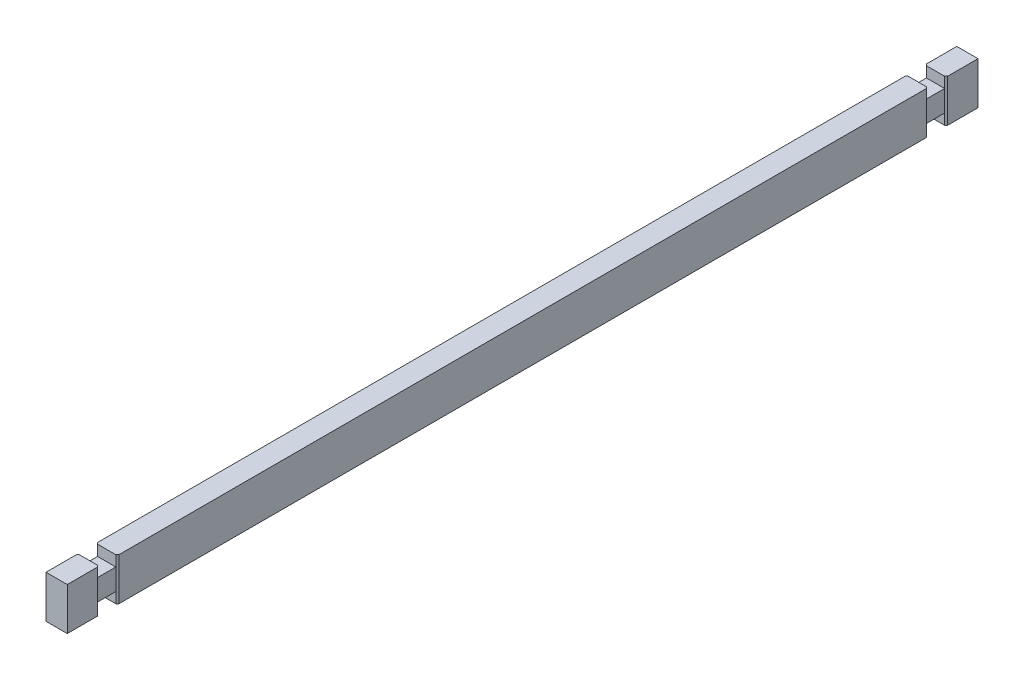
SolidWorks part; units mm, degrees
ref_plane "Front Plane" through (0, 0, 0) normal (0, 0, 1) x (1, 0, 0)
ref_plane "Top Plane" through (0, 0, 0) normal (0, 1, 0) x (1, 0, 0)
ref_plane "Right Plane" through (0, 0, 0) normal (1, 0, 0) x (0, 0, -1)
sketch "Sketch1" plane through (0, 0, 0) normal (0, 0, 1) x (1, 0, 0)
  line L1 (-35, 70) -> (35, 70)
  line L2 (-35, 70) -> (-35, -70)
  line L3 (-35, -70) -> (35, -70)
  line L4 (35, 70) -> (35, -70)
  dimension "D1" = 140
  dimension "D2" = 70
  dimension "D3" = 35
  dimension "D4" = 70
extrude "Extrude1" add sketch "Sketch1" along normal blind 3000
sketch "Sketch2" plane through (0, 70, 0) normal (0, 1, 0) x (-1, 0, 0)
  line L0 (35, 100) -> (30, 105)
  line L1 (35, 3000) -> (35, 0) construction
  line L2 (30, 165) -> (30, 105)
  line L3 (30, 165) -> (35, 170)
  line L4 (-35, 100) -> (-30, 105)
  line L5 (-35, 3000) -> (-35, 0) construction
  line L6 (-30, 105) -> (-30, 165)
  line L7 (-30, 165) -> (-35, 170)
  line L8 (-35, 100) -> (-35, 170)
  line L9 (35, 100) -> (35, 170)
  line L10 (-35, 0) -> (35, 0) construction
  dimension "D1" = 70
  dimension "D2" = 60
  dimension "D3" = 5
  dimension "D4" = 60
  dimension "D5" = 70
  dimension "D6" = 5
  dimension "D7" = 100
  dimension "D8" = 100
  dimension "D9" = 45
  dimension "D10" = 45
extrude "Cut-Extrude1" cut sketch "Sketch2" against normal through all
sketch "Sketch3" plane through (30, 0, 0) normal (1, 0, 0) x (0, 0, -1)
  line L0 (-105, -70) -> (-105, 70) construction
  line L1 (-165, 70) -> (-105, 70)
  line L2 (-165, 70) -> (-165, 35)
  line L3 (-165, 35) -> (-105, 35)
  line L4 (-105, 70) -> (-105, 35)
  line L5 (-165, -70) -> (-165, 70) construction
  line L6 (-165, -35) -> (-105, -35)
  line L7 (-165, -35) -> (-165, -70)
  line L8 (-165, -70) -> (-105, -70)
  line L9 (-105, -35) -> (-105, -70)
  dimension "D1" = 35
  dimension "D2" = 35
extrude "Cut-Extrude2" cut sketch "Sketch3" against normal through all
sketch "Sketch4" plane through (0, 70, 0) normal (0, 1, 0) x (-1, 0, 0)
  line L1 (-35, 3000) -> (-35, 170) construction
  line L2 (-35, 2830) -> (-35, 2900)
  line L3 (-35, 2900) -> (-30, 2895)
  line L4 (-30, 2895) -> (-30, 2835)
  line L6 (-30, 2835) -> (-35, 2830)
  line L7 (35, 2830) -> (30, 2835)
  line L8 (35, 3000) -> (35, 170) construction
  line L9 (30, 2835) -> (30, 2895)
  line L10 (30, 2895) -> (35, 2900)
  line L11 (35, 2900) -> (35, 2830)
  dimension "D1" = 100
  dimension "D2" = 5
  dimension "D3" = 60
  dimension "D4" = 70
  dimension "D5" = 70
  dimension "D6" = 60
  dimension "D7" = 5
  dimension "D8" = 100
extrude "Cut-Extrude3" cut sketch "Sketch4" against normal through all
sketch "Sketch5" plane through (30, 0, 0) normal (1, 0, 0) x (0, 0, -1)
  line L0 (-2835, -70) -> (-2835, 70) construction
  line L1 (-2895, 70) -> (-2835, 70)
  line L2 (-2895, 70) -> (-2895, 35)
  line L3 (-2895, 35) -> (-2835, 35)
  line L4 (-2835, 70) -> (-2835, 35)
  line L6 (-2895, -70) -> (-2835, -70)
  line L7 (-2895, -70) -> (-2895, -35)
  line L8 (-2895, -35) -> (-2835, -35)
  line L9 (-2835, -70) -> (-2835, -35)
  dimension "D1" = 35
  dimension "D2" = 35
extrude "Cut-Extrude4" cut sketch "Sketch5" against normal through all
